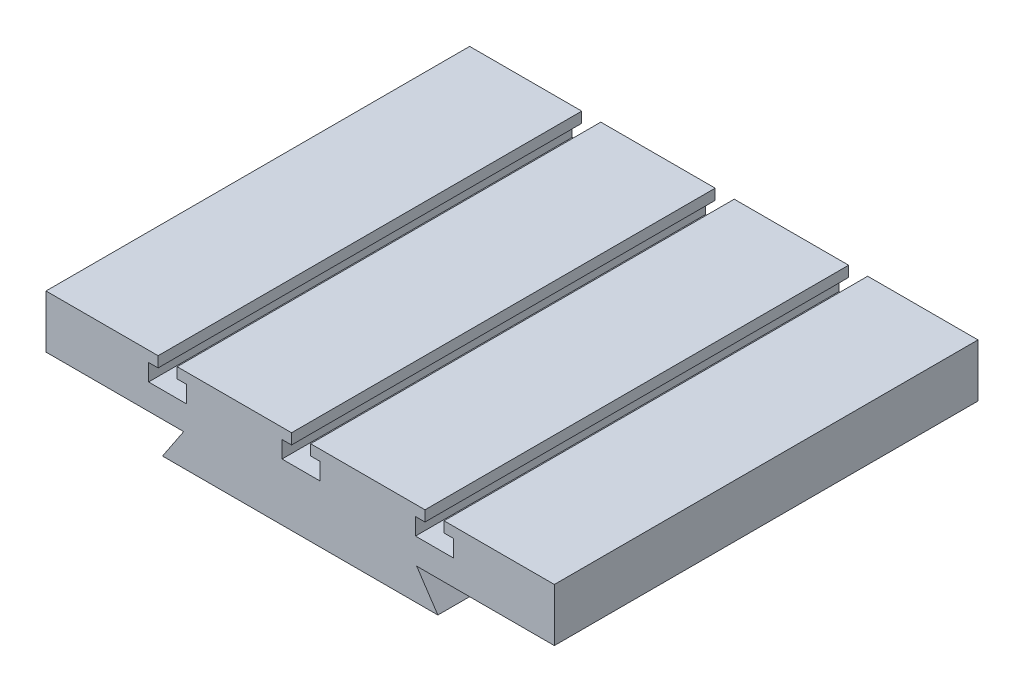
SolidWorks part; units mm, degrees
ref_plane "Спереди" through (0, 0, 0) normal (0, 0, 1) x (1, 0, 0)
ref_plane "Сверху" through (0, 0, 0) normal (0, 1, 0) x (1, 0, 0)
ref_plane "Справа" through (0, 0, 0) normal (1, 0, 0) x (0, 0, -1)
sketch "Эскиз1" plane through (0, 0, 0) normal (0, 0, 1) x (1, 0, 0)
  line L0 (0, 0) -> (65, 0)
  line L1 (65, 0) -> (55, 15)
  line L2 (55, 15) -> (120, 15)
  line L3 (120, 15) -> (120, 40)
  line L4 (120, 40) -> (0, 40)
  line L5 (0, 56.4782) -> (0, 0) construction
  line L6 (-120, 40) -> (0, 40)
  line L7 (-120, 15) -> (-120, 40)
  line L8 (-55, 15) -> (-120, 15)
  line L9 (-65, 0) -> (-55, 15)
  line L10 (0, 0) -> (-65, 0)
  line L11 (-75, 0) -> (75, 0) construction
  dimension "D1" = 25
  dimension "D2" = 65
  dimension "D3" = 120
extrude "Бобышка-Вытянуть1" add sketch "Эскиз1" along normal blind 200
sketch "Эскиз2" plane through (0, 0, 200) normal (0, 0, 1) x (1, 0, 0)
  line L0 (-8.5738, 27) -> (9.4262, 27)
  line L1 (9.4262, 27) -> (9.4262, 35)
  line L2 (9.4262, 35) -> (4.9262, 35)
  line L3 (4.9262, 35) -> (4.9262, 40)
  line L4 (120, 40) -> (-120, 40) construction
  line L5 (4.9262, 40) -> (-4.0738, 40)
  line L6 (-4.0738, 40) -> (-4.0738, 35)
  line L7 (-4.0738, 35) -> (-8.5738, 35)
  line L8 (-8.5738, 35) -> (-8.5738, 27)
  line L9 (54.4262, 27) -> (72.4262, 27)
  line L10 (72.4262, 27) -> (72.4262, 35)
  line L11 (72.4262, 35) -> (67.9262, 35)
  line L12 (67.9262, 35) -> (67.9262, 40)
  line L13 (67.9262, 40) -> (58.9262, 40)
  line L14 (58.9262, 40) -> (58.9262, 35)
  line L15 (58.9262, 35) -> (54.4262, 35)
  line L16 (54.4262, 35) -> (54.4262, 27)
  line L17 (-71.5738, 27) -> (-53.5738, 27)
  line L18 (-53.5738, 27) -> (-53.5738, 35)
  line L19 (-53.5738, 35) -> (-58.0738, 35)
  line L20 (-58.0738, 35) -> (-58.0738, 40)
  line L21 (-58.0738, 40) -> (-67.0738, 40)
  line L22 (-67.0738, 40) -> (-67.0738, 35)
  line L23 (-67.0738, 35) -> (-71.5738, 35)
  line L24 (-71.5738, 35) -> (-71.5738, 27)
  point P3 (0.4262, 27)
  point P15 (63.4262, 27)
  point P23 (-62.5738, 27)
  dimension "D1" = 18
  dimension "D2" = 9
  dimension "D3" = 5
  dimension "D4" = 8
  dimension "D5" = 2
  dimension "D6" = 2
extrude "Вырез-Вытянуть1" cut sketch "Эскиз2" against normal through all
